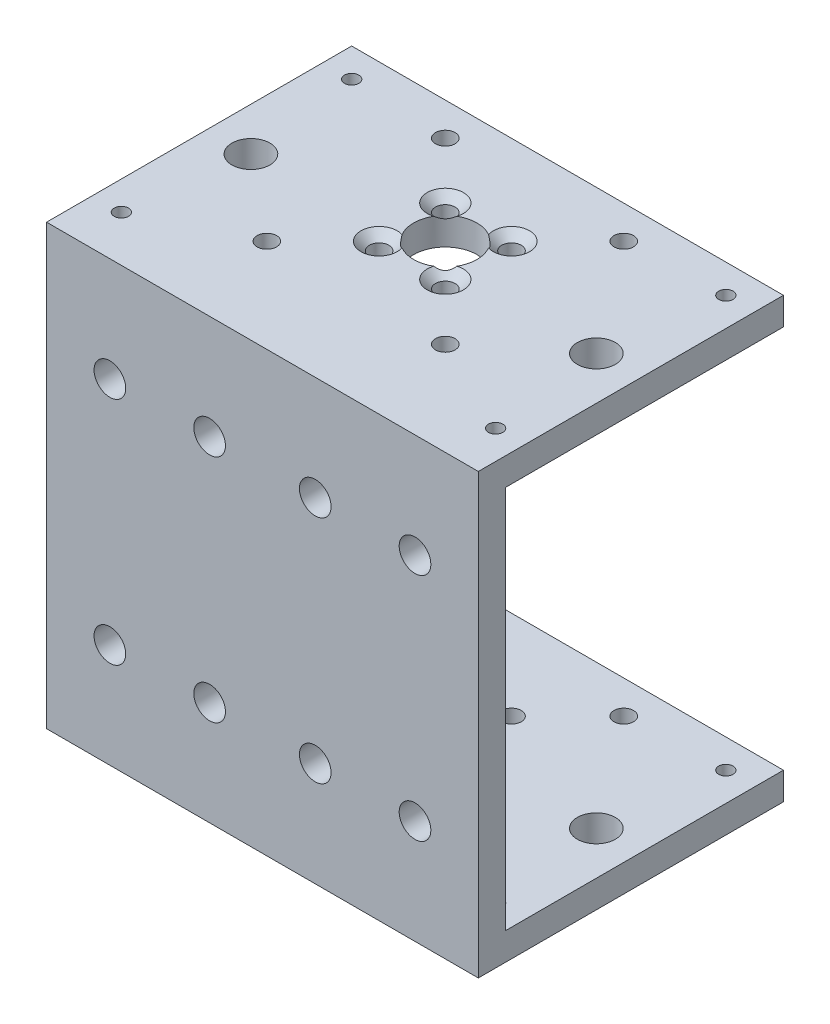
SolidWorks part; units mm, degrees
ref_plane "Front Plane" through (0, 0, 0) normal (0, 0, 1) x (1, 0, 0)
ref_plane "Top Plane" through (0, 0, 0) normal (0, 1, 0) x (1, 0, 0)
ref_plane "Right Plane" through (0, 0, 0) normal (1, 0, 0) x (0, 0, -1)
sketch "Sketch3" plane through (0, 0, 0) normal (1, 0, 0) x (0, 0, -1)
  line L0 (0, 0) -> (0, 76.2)
  line L1 (0, 0) -> (53, 0)
  line L2 (0, 76.2) -> (53, 76.2)
  dimension "D1" = 76.2
  dimension "D2" = 53
extrude "Extrude-Thin1" add sketch "Sketch3" along normal mid plane 75 thin
sketch "Sketch4" plane through (0, 4.7625, 0) normal (0, 1, 0) x (1, 0, 0)
  line L0 (37.5, 4.7625) -> (-37.5, 4.7625) construction
  circle A0 centre (0, 31.7625) radius 5.5
  dimension "D2" = 11
  dimension "D1" = 27
extrude "Cut-Extrude1" cut sketch "Sketch4" against normal through all both and the other way through all
hole_wizard "M5 Clearance Hole1" positions "Sketch5" profile "Sketch7" hole size "M5" standard "ANSI Metric" end condition through all
sketch "Sketch5" plane through (0, 0, 0) normal (0, 0, 1) x (1, 0, 0)
  point P0 (-26.5, 58.1005)
  point P2 (26.5, 58.1005)
  point P4 (26.5, 18.1005)
  point P7 (-26.5, 18.1005)
sketch "Sketch7" plane through (-26.5, 58.1005, 0) normal (1, 0, 0) x (0, -1, 0)
  line L0 (0, 0) -> (0, 53)
  line L1 (0, 53) -> (2.75, 53)
  line L2 (2.75, 53) -> (2.75, 0)
  line L5 (2.75, 0) -> (0, 0)
  line L11 (0, -6.35) -> (0, 107.95) construction
  dimension "Thru Hole Dia." = 5.5
  dimension "Thru Hole Depth" = 53
hole_wizard "M6 Clearance Hole2" positions "Sketch8" profile "Sketch9" hole size "M6" standard "ANSI Metric" end condition through all
sketch "Sketch8" plane through (0, 0, 0) normal (0, -1, 0) x (-1, 0, 0)
  line L0 (-37.5, 53) -> (37.5, 53) construction
  line L1 (0, 0) -> (0, 53) construction
  line L2 (-37.5, 0) -> (37.5, 0) construction
  point P0 (30, 28)
  point P2 (-30, 28)
  dimension "D1" = 25
  dimension "D2" = 60
sketch "Sketch9" plane through (-30, 0, -28) normal (1, 0, 0) x (0, 0, -1)
  line L0 (0, 0) -> (0, 76.2)
  line L1 (0, 76.2) -> (3.3, 76.2)
  line L2 (3.3, 76.2) -> (3.3, 0)
  line L5 (3.3, 0) -> (0, 0)
  line L11 (0, -6.35) -> (0, 107.95) construction
  dimension "Thru Hole Dia." = 6.6
  dimension "Thru Hole Depth" = 76.2
hole_wizard "CSK for M3 Flat Head Machine Screw1" positions "Sketch10" profile "Sketch11" countersink size "M3" standard "ANSI Metric"
sketch "Sketch10" plane through (0, 0, 0) normal (0, -1, 0) x (-1, 0, 0)
  point P0 (5.75, 26.0125)
  point P3 (-5.75, 26.0125)
  point P6 (-5.75, 37.5125)
  point P9 (5.75, 37.5125)
sketch "Sketch11" plane through (-5.75, 0, -26.0125) normal (1, 0, 0) x (0, 0, -1)
  line L0 (0, 0) -> (0, 11.0215)
  line L1 (0, 11.0215) -> (1.7, 10)
  line L2 (1.7, 10) -> (1.7, 1.45)
  line L3 (1.7, 1.45) -> (3.15, 0)
  line L5 (3.15, 0) -> (0, 0)
  line L6 (-1.7, 1.45) -> (-3.15, 0) construction
  line L10 (0, 11.0215) -> (-1.7, 10) construction
  line L11 (0, -6.35) -> (0, 107.95) construction
  dimension "Hole Dia." = 3.4
  dimension "Hole Depth" = 10
  dimension "Near C'Sink Dia." = 6.3
  dimension "Near C'Sink Angle" = 90
  dimension "Drill Angle" = 118
ref_plane "Plane2" through (0, 38.1, 0) normal (0, -1, 0) x (-1, 0, 0)
mirror "Mirror1" about plane through (0, 38.1, 0) normal (0, -1, 0) of "CSK for M3 Flat Head Machine Screw1"
hole_wizard "CSK for M3 SFHCS2" positions "Sketch12" profile "Sketch13" countersink size "M3" standard "ANSI Metric"
sketch "Sketch12" plane through (0, 71.4375, 0) normal (0, -1, 0) x (-1, 0, 0)
  point P0 (15.5, 47.2625)
  point P3 (15.5, 16.2625)
  point P6 (-15.5, 16.2625)
  point P9 (-15.5, 47.2625)
sketch "Sketch13" plane through (-15.5, 71.4375, -47.2625) normal (1, 0, 0) x (0, 0, -1)
  line L0 (0, 0) -> (0, 11.0215)
  line L1 (0, 11.0215) -> (1.7, 10)
  line L2 (1.7, 10) -> (1.7, 1.66)
  line L3 (1.7, 1.66) -> (3.36, 0)
  line L5 (3.36, 0) -> (0, 0)
  line L6 (-1.7, 1.66) -> (-3.36, 0) construction
  line L10 (0, 11.0215) -> (-1.7, 10) construction
  line L11 (0, -6.35) -> (0, 107.95) construction
  dimension "Hole Dia." = 3.4
  dimension "Hole Depth" = 10
  dimension "Near C'Sink Dia." = 6.72
  dimension "Near C'Sink Angle" = 90
  dimension "Drill Angle" = 118
hole_wizard "M3 Clearance Hole1" positions "Sketch14" profile "Sketch16" hole size "M3" standard "ANSI Metric" end condition through all
sketch "Sketch14" plane through (0, 76.2, 0) normal (0, 1, 0) x (1, 0, 0)
  point P0 (-15.5, 47.2625)
  point P3 (15.5, 47.2625)
  point P6 (15.5, 16.2625)
  point P9 (-15.5, 16.2625)
sketch "Sketch16" plane through (-15.5, 76.2, -47.2625) normal (1, 0, 0) x (0, 0, 1)
  line L0 (0, 0) -> (0, 76.2)
  line L1 (0, 76.2) -> (1.7, 76.2)
  line L2 (1.7, 76.2) -> (1.7, 0)
  line L5 (1.7, 0) -> (0, 0)
  line L11 (0, -6.35) -> (0, 107.95) construction
  dimension "Thru Hole Dia." = 3.4
  dimension "Thru Hole Depth" = 76.2
hole_wizard "M3x0.5 Tapped Hole2" positions "Sketch17" profile "Sketch19" tap size "M3x0.5" standard "ANSI Metric"
sketch "Sketch17" plane through (0, 76.2, 0) normal (0, 1, 0) x (1, 0, 0)
  point P0 (-32.5, 48)
  point P3 (32.5, 48)
  point P6 (32.5, 8)
  point P9 (-32.5, 8)
sketch "Sketch19" plane through (-32.5, 76.2, -48) normal (1, 0, 0) x (0, 0, 1)
  line L0 (0, 0) -> (0, 8.2511)
  line L1 (0, 8.2511) -> (1.25, 7.5)
  line L2 (1.25, 7.5) -> (1.25, 0)
  line L5 (1.25, 0) -> (0, 0)
  line L10 (0, 8.2511) -> (-1.25, 7.5) construction
  line L11 (0, -6.35) -> (0, 107.95) construction
  dimension "Tap Drill Dia." = 2.5
  dimension "Tap Drill Depth" = 7.5
  dimension "Drill Angle" = 118
cosmetic thread "Hole Thread5" parameters "D1"=5, "D2"=3
cosmetic thread "Hole Thread6" parameters "D1"=5, "D2"=3
cosmetic thread "Hole Thread7" parameters "D1"=5, "D2"=3
cosmetic thread "Hole Thread8" parameters "D1"=5, "D2"=3
mirror "Mirror2" about plane through (0, 38.1, 0) normal (0, -1, 0) of "M3x0.5 Tapped Hole2"
cosmetic thread "Hole Thread9" parameters "D1"=5, "D2"=3
cosmetic thread "Hole Thread10" parameters "D1"=5, "D2"=3
cosmetic thread "Hole Thread11" parameters "D1"=5, "D2"=3
cosmetic thread "Hole Thread12" parameters "D1"=5, "D2"=3
hole_wizard "M5 Clearance Hole2" positions "Sketch20" profile "Sketch22" hole size "M5" standard "ANSI Metric" end condition through all
sketch "Sketch20" plane through (0, 0, 0) normal (0, 0, 1) x (1, 0, 0)
  line L0 (0, 0) -> (0, 76.2) construction
  line L1 (37.5, 76.2) -> (-37.5, 76.2) construction
  point P0 (-9.175, 18.1)
  point P4 (-9.175, 58.1)
  point P13 (9.175, 58.1)
  point P15 (9.175, 18.1)
  point P20 (-9.175, 58.1)
  point P21 (-9.175, 38.1)
  point P22 (-9.175, 18.1)
sketch "Sketch22" plane through (-9.175, 18.1, 0) normal (1, 0, 0) x (0, -1, 0)
  line L0 (0, 0) -> (0, 53)
  line L1 (0, 53) -> (2.75, 53)
  line L2 (2.75, 53) -> (2.75, 0)
  line L5 (2.75, 0) -> (0, 0)
  line L11 (0, -6.35) -> (0, 107.95) construction
  dimension "Thru Hole Dia." = 5.5
  dimension "Thru Hole Depth" = 53
